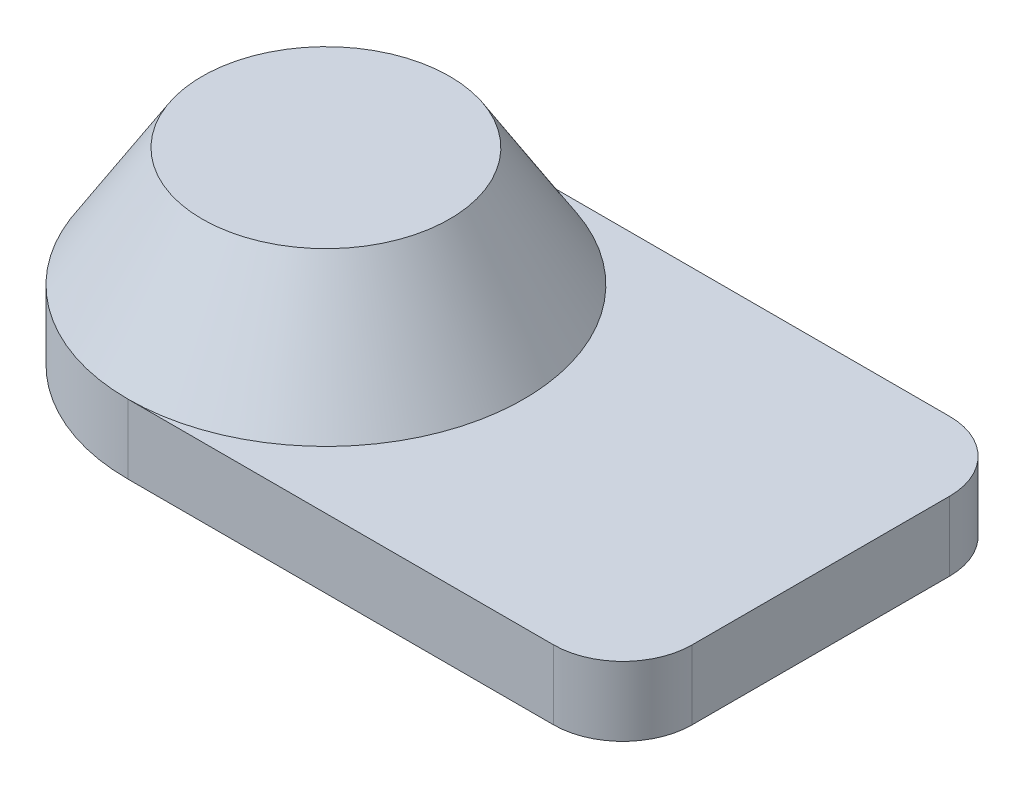
SolidWorks part; units mm, degrees
ref_plane "Front Plane" through (0, 0, 0) normal (0, 0, 1) x (1, 0, 0)
ref_plane "Top Plane" through (0, 0, 0) normal (0, 1, 0) x (1, 0, 0)
ref_plane "Right Plane" through (0, 0, 0) normal (1, 0, 0) x (0, 0, -1)
sketch "Sketch1" plane through (0, 0, 0) normal (0, 1, 0) x (1, 0, 0)
  line L1 (0, 0) -> (63.5, 0)
  line L3 (0, 50.8) -> (63.5, 50.8)
  line L4 (63.5, 0) -> (63.5, 50.8)
  arc A0 (0, 50.8) -> (0, 0) centre (0, 25.4) ccw
  dimension "D1" = 63.5
  dimension "D2" = 50.8
extrude "Boss-Extrude1" add sketch "Sketch1" along normal blind 8.89
fillet "Fillet1" radius 8.89 2 edges at (63.5, 4.445, -50.8) (63.5, 4.445, 0)
sketch "Sketch4" plane through (0, 8.89, 0) normal (0, 1, 0) x (1, 0, 0)
  line L0 (0, 50.8) -> (0, 0) construction
  circle A0 centre (0, 25.4) radius 25.4
  dimension "D1" = 50.8
ref_plane "Plane1" through (0, 24.13, 0) normal (0, 1, 0) x (1, 0, 0)
sketch "Sketch11" plane through (0, 24.13, 0) normal (0, 1, 0) x (1, 0, 0)
  circle A0 centre (0, 25.4) radius 15.875
  dimension "D1" = 31.75
loft "Loft2" add profiles "Sketch4", "Sketch11"
